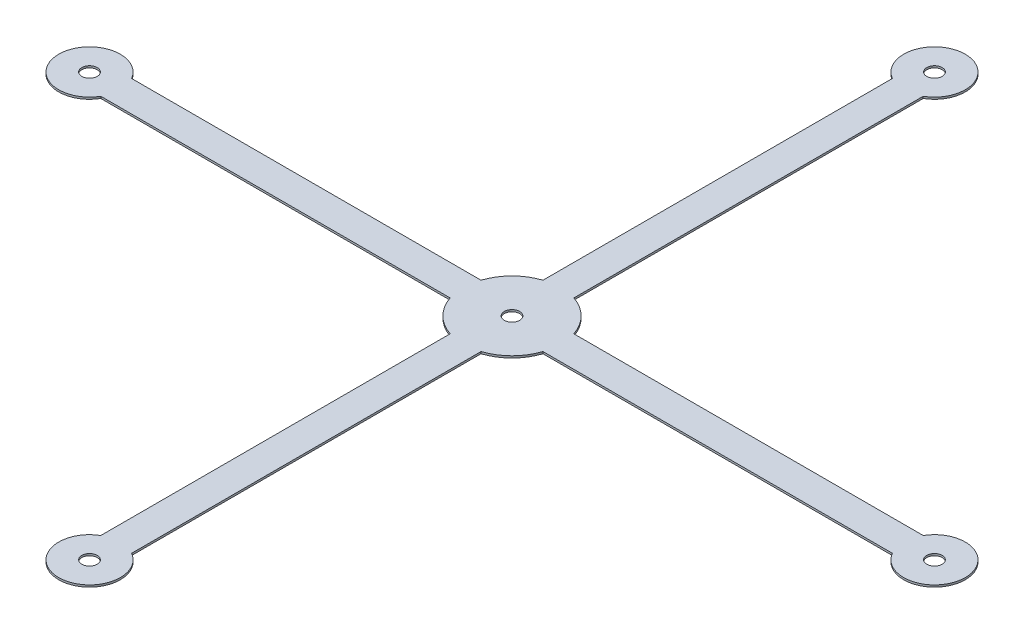
SolidWorks part; units mm, degrees
ref_plane "Front Plane" through (0, 0, 0) normal (0, 0, 1) x (1, 0, 0)
ref_plane "Top Plane" through (0, 0, 0) normal (0, 1, 0) x (1, 0, 0)
ref_plane "Right Plane" through (0, 0, 0) normal (1, 0, 0) x (0, 0, -1)
sketch "Sketch1" plane through (0, 0, 0) normal (0, 1, 0) x (1, 0, 0)
  line L0 (0, 0) -> (-54.864, 0) construction
  line L1 (-54.864, 4) -> (-4.9318, 4)
  line L3 (-4.9318, -4) -> (-54.864, -4)
  line L4 (-4, 4.9318) -> (-4, 54.864)
  line L5 (4, 54.864) -> (4, 4.9318)
  line L6 (4.9318, 4) -> (54.864, 4)
  line L7 (54.864, -4) -> (4.9318, -4)
  line L8 (4, -4.9318) -> (4, -54.864)
  line L9 (-4, -54.864) -> (-4, -4.9318)
  circle A0 centre (-54.864, 0) radius 1
  arc A1 (4, 54.864) -> (-4, 54.864) centre (0, 54.864) ccw
  circle A2 centre (0, 54.864) radius 1
  arc A3 (54.864, -4) -> (54.864, 4) centre (54.864, 0) ccw
  arc A4 (-54.864, 4) -> (-54.864, -4) centre (-54.864, 0) ccw
  circle A5 centre (54.864, 0) radius 1
  arc A6 (-4, -54.864) -> (4, -54.864) centre (0, -54.864) ccw
  circle A7 centre (0, -54.864) radius 1
  arc A8 (4.9318, 4) -> (4, 4.9318) centre (0, 0) ccw
  arc A9 (-4, 4.9318) -> (-4.9318, 4) centre (0, 0) ccw
  arc A10 (-4.9318, -4) -> (-4, -4.9318) centre (0, 0) ccw
  arc A11 (4, -4.9318) -> (4.9318, -4) centre (0, 0) ccw
  point P6 (-55.864, 0)
  point P12 (0, 0)
  point P13 (-58.864, 0)
  point P32 (0, 0)
  dimension "D1" = 2
  dimension "D5" = 12.7
  dimension "D2" = 54.864
  dimension "D4" = 3
  dimension "D3" = 4
extrude "Boss-Extrude1" add sketch "Sketch1" along normal blind 0.254
sketch "Sketch2" plane through (0, 0.254, 0) normal (0, 1, 0) x (1, 0, 0)
  line L0 (0, -54.864) -> (0, 0) construction
  line L1 (-2, -51.3999) -> (-2, -6.0268)
  line L2 (2, -51.3999) -> (2, -6.0268)
  line L3 (4, -54.864) -> (4, -4.9318)
  line L4 (-54.864, 4) -> (-4.9318, 4)
  line L5 (-4, -54.864) -> (-4, -4.9318)
  line L6 (-51.3999, 2) -> (-6.0268, 2)
  line L7 (-51.3999, -2) -> (-6.0268, -2)
  line L8 (-54.864, -4) -> (-4.9318, -4)
  line L9 (4, 54.864) -> (4, 4.9318)
  line L10 (2, 51.3999) -> (2, 6.0268)
  line L11 (-2, 51.3999) -> (-2, 6.0268)
  line L12 (-4, 54.864) -> (-4, 4.9318)
  line L13 (54.864, -4) -> (4.9318, -4)
  line L14 (51.3999, -2) -> (6.0268, -2)
  line L15 (51.3999, 2) -> (6.0268, 2)
  line L16 (54.864, 4) -> (4.9318, 4)
  arc A0 (2, -6.0268) -> (4, -4.9318) centre (0, 0) ccw
  arc A1 (4, -54.864) -> (2, -51.3999) centre (0, -54.864) ccw
  arc A2 (-2, -51.3999) -> (-4, -54.864) centre (0, -54.864) ccw
  arc A3 (-4, -4.9318) -> (-2, -6.0268) centre (0, 0) ccw
  arc A4 (-51.3999, 2) -> (-54.864, 4) centre (-54.864, 0) ccw
  arc A5 (-4.9318, 4) -> (-6.0268, 2) centre (0, 0) ccw
  arc A6 (-6.0268, -2) -> (-4.9318, -4) centre (0, 0) ccw
  arc A7 (-54.864, -4) -> (-51.3999, -2) centre (-54.864, 0) ccw
  arc A8 (2, 51.3999) -> (4, 54.864) centre (0, 54.864) ccw
  arc A9 (4, 4.9318) -> (2, 6.0268) centre (0, 0) ccw
  arc A10 (-2, 6.0268) -> (-4, 4.9318) centre (0, 0) ccw
  arc A11 (-4, 54.864) -> (-2, 51.3999) centre (0, 54.864) ccw
  arc A12 (51.3999, -2) -> (54.864, -4) centre (54.864, 0) ccw
  arc A13 (4.9318, -4) -> (6.0268, -2) centre (0, 0) ccw
  arc A14 (6.0268, 2) -> (4.9318, 4) centre (0, 0) ccw
  arc A15 (54.864, 4) -> (51.3999, 2) centre (54.864, 0) ccw
  circle A16 centre (0, 0) radius 1
  circle A17 centre (-54.864, 0) radius 1 construction
  point P46 (0, 0)
  dimension "D1" = 4
  dimension "D2" = 4
extrude "Cut-Extrude1" cut sketch "Sketch2" against normal blind 10
equation "\"orig_diameter\"= 50.8mm"
equation "\"scale_factor\"= 1.08"
equation "\"d\"= \"orig_diameter\" * \"scale_factor\""
equation "\"D2@Sketch1\"=\"d\""
